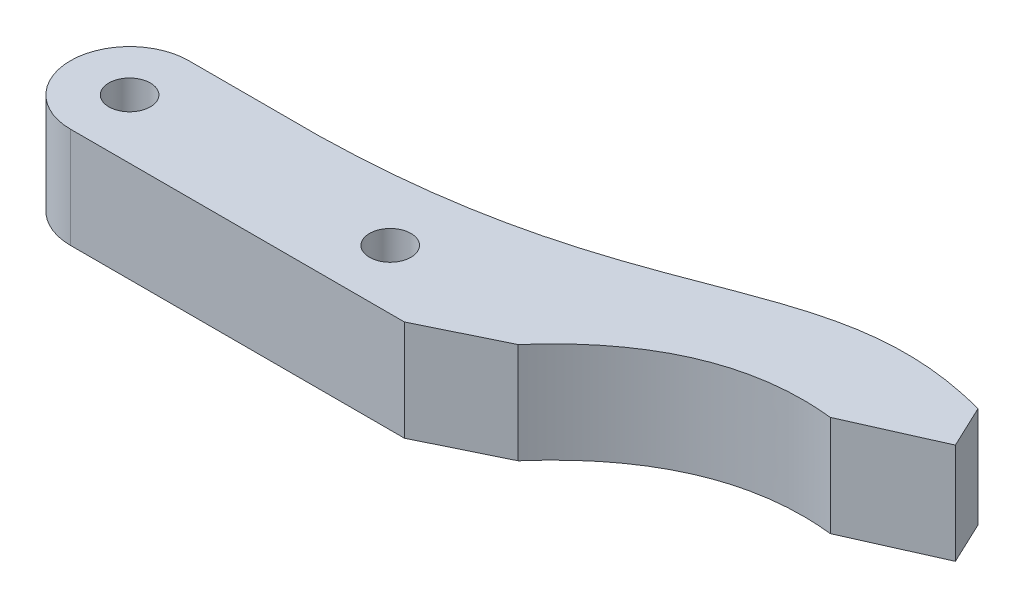
SolidWorks part; units mm, degrees
ref_plane "Front Plane" through (0, 0, 0) normal (0, 0, 1) x (1, 0, 0)
ref_plane "Top Plane" through (0, 0, 0) normal (0, 1, 0) x (1, 0, 0)
ref_plane "Right Plane" through (0, 0, 0) normal (1, 0, 0) x (0, 0, -1)
sketch "Sketch1" plane through (0, 0, 0) normal (0, 1, 0) x (1, 0, 0)
  line L1 (-5000, 5000) -> (27000, 5000)
  line L2 (-5000, 5000) -> (-5000, -5000)
  line L3 (-5000, -5000) -> (27000, -5000)
  line L4 (27000, 5000) -> (27000, -5000)
  line L5 (-5000, 5000) -> (27000, -5000) construction
  line L6 (-5000, -5000) -> (27000, 5000) construction
  circle A0 centre (0, 0) radius 1750
  circle A1 centre (0, 0) radius 5000
  circle A2 centre (22000, 0) radius 1750
  circle A3 centre (22000, 0) radius 5000
  point P7 (11000, 0)
  dimension "D1" = 10000
  dimension "D2" = 22000
  dimension "D3" = 3500
extrude "Boss-Extrude1" add sketch "Sketch1" along normal blind 8500 contours A1 A0 | A3 L1 A1 L3 | A3 A2
sketch "Sketch2" plane through (0, 8500, 0) normal (0, 1, 0) x (1, 0, 0)
  line L0 (22000, -5000) -> (28197.4097, -5000)
  line L1 (28197.4097, -5000) -> (34649.3569, -1853.1751)
  line L2 (11000, 5000) -> (22000, 5000)
  line L4 (0, 5000) -> (22000, 5000) construction
  line L5 (58750, 12870) -> (60457.635, 9252.8212)
  line L6 (60457.635, 9252.8212) -> (53148.7942, 6000)
  line L7 (0, -5000) -> (22000, -5000) construction
  circle A0 centre (22000, 0) radius 1750 construction
  arc A1 (22000, -5000) -> (22000, 5000) centre (22000, 0) ccw construction
  arc A2 (22000, -5000) -> (22000, 5000) centre (22000, 0) ccw
  spline S0 degree 3 poles (11000, 5000) (38094.6691, 5526.9476) (42172.4966, 17338.223) (58750, 12870) knots 0 0 0 0 1 1 1 1
  spline S1 degree 2 poles (34649.3569, -1853.1751) (42552.502, 7200.8713) (53148.7942, 6000) knots 0 0 0 1 1 1
  point P16 (28961.5031, 9297.654)
  point P17 (54922.168, 6000)
  point P18 (30281.4261, 9186.7724)
  point P19 (49503.2497, 5608.2415)
  point P20 (58750, 9186.7724)
  point P21 (60457.635, 9186.7724)
  point P22 (48480.8123, 6017.2164)
  point P23 (34649.3569, 9252.8212)
  point P25 (28197.4097, -5000)
  point P26 (28197.4097, -5000)
  point P29 (28197.4097, -5000)
  point P30 (28197.4097, -5000)
  dimension "D7" = 6197.4097
  dimension "D1" = 4000
  dimension "D2" = 8000
  dimension "D3" = 17870
  dimension "D4" = 11000
  dimension "D5" = 26
  dimension "D6" = 36750
  dimension "D8" = 12649.3569
  dimension "D9" = 26480.8123
  dimension "D10" = 31148.7942
  dimension "D11" = 11017.2164
extrude "Boss-Extrude2" add sketch "Sketch2" against normal blind 8500 contours L2 A2 L0 L1 S1 L6 L5 S0
